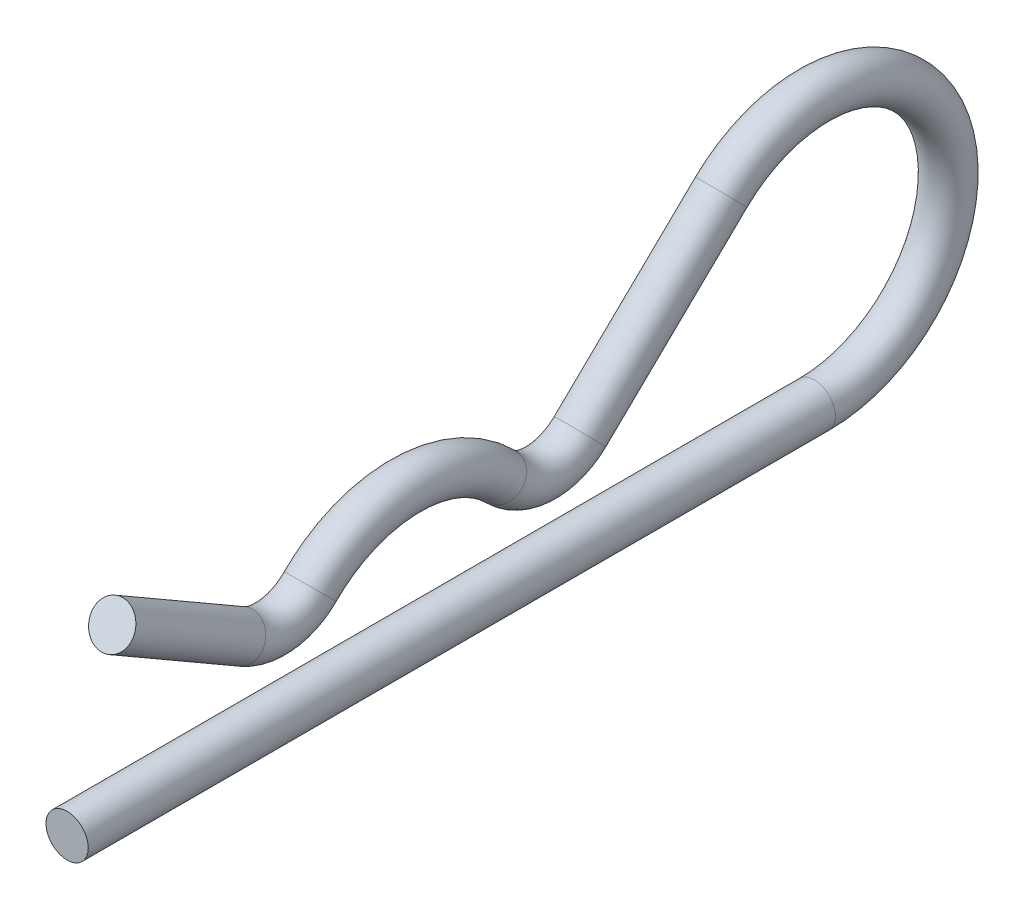
SolidWorks part; units mm, degrees
ref_plane "Front" through (0, 0, 0) normal (0, 0, 1) x (1, 0, 0)
ref_plane "Top" through (0, 0, 0) normal (0, 1, 0) x (1, 0, 0)
ref_plane "Right" through (0, 0, 0) normal (1, 0, 0) x (0, 0, -1)
sketch "Sketch1" plane through (0, 0, 0) normal (0, 0, 1) x (1, 0, 0)
  circle A0 centre (0, 0) radius 0.5953
  dimension "WireOD" = 1.1906
sketch "Sketch2" plane through (0, 0, 0) normal (1, 0, 0) x (0, 0, -1)
  line L0 (0, 0) -> (21.0344, 0)
  line L1 (5.7183, 3.7703) -> (13.3317, 3.7703) construction
  line L2 (25.4, 0) -> (25.4, 3.7703) construction
  line L3 (25.4, 3.7703) -> (24.8047, 3.7703) construction
  line L5 (25.4, 0) -> (0, 0) construction
  line L6 (4.9246, 2.3955) -> (1.27, 4.5055)
  line L7 (9.525, 3.7703) -> (9.525, 0) construction
  line L13 (18.4118, 6.4791) -> (14.4359, 2.6298)
  circle A0 centre (21.0344, 3.7703) radius 3.175 construction
  arc A1 (12.2038, 2.6532) -> (6.8462, 2.6532) centre (9.525, 0) ccw
  arc A6 (6.8462, 2.6532) -> (4.9246, 2.3955) centre (5.7183, 3.7703) cw
  arc A8 (14.4359, 2.6298) -> (12.2038, 2.6532) centre (13.3317, 3.7703) cw
  arc A9 (21.0344, 0) -> (18.4118, 6.4791) centre (21.0344, 3.7703) ccw
  dimension "D2" = 9.525
  dimension "D1" = 1.5875
  dimension "D11" = 0.5953
  dimension "EyeID" = 6.35
  dimension "D3" = 0.5953
  dimension "D5" = 1.27
  dimension "D9" = 30
  dimension "Length" = 25.4
sweep "Sweep1" add profiles "Sketch1" path "Sketch2"
equation "\"D11@Sketch2\" = \"WireOD@Sketch1\"/2"
equation "\"D1@Sketch2\" = \"EyeID@Sketch2\"/4"
equation "\"D3@Sketch2\" = \"D11@Sketch2\""
equation "\"D2@Sketch2\" = (\"Length@Sketch2\"-\"EyeID@Sketch2\")/2"
equation "\"D5@Sketch2\" = \"Length@Sketch2\"*.05"
